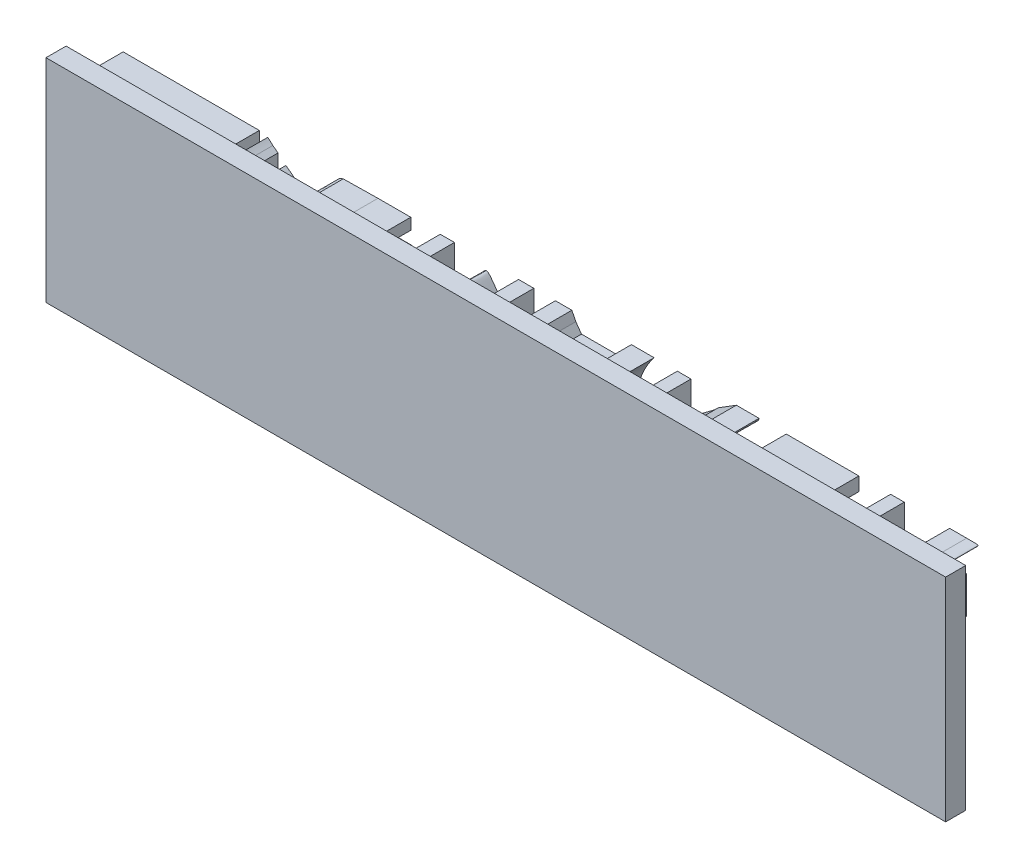
SolidWorks part; units mm, degrees
ref_plane "Front Plane" through (0, 0, 0) normal (0, 0, 1) x (1, 0, 0)
ref_plane "Top Plane" through (0, 0, 0) normal (0, 1, 0) x (1, 0, 0)
ref_plane "Right Plane" through (0, 0, 0) normal (1, 0, 0) x (0, 0, -1)
sketch "Sketch1" plane through (0, 0, 0) normal (0, 0, 1) x (1, 0, 0)
  line L3 (5.334, 288.4593) -> (5.0518, 287.3304)
  line L4 (5.0518, 287.3304) -> (5.0518, 276.606)
  line L5 (5.0518, 276.606) -> (5.0518, 266.4178)
  line L6 (5.0518, 266.4178) -> (5.334, 265.0067)
  line L7 (7.5918, 263.0311) -> (8.7207, 262.4667)
  line L8 (8.7207, 262.4667) -> (23.7349, 262.4667)
  line L9 (23.7349, 262.4667) -> (38.6644, 262.4667)
  line L10 (38.6644, 262.4667) -> (39.7933, 263.0311)
  line L11 (42.3333, 272.6549) -> (42.3333, 279.4282)
  line L12 (42.3333, 279.4282) -> (27.1498, 279.4282)
  line L13 (27.1498, 279.4282) -> (11.9944, 279.4282)
  line L14 (11.9944, 279.4282) -> (11.9944, 282.5327)
  line L15 (11.9944, 282.5327) -> (11.9944, 285.6371)
  line L16 (11.9944, 285.6371) -> (27.1498, 285.6371)
  line L17 (27.1498, 285.6371) -> (42.3333, 285.6371)
  line L18 (42.3333, 285.6371) -> (42.3333, 288.4593)
  line L19 (42.3333, 288.4593) -> (42.3333, 291.2816)
  line L20 (42.3333, 291.2816) -> (26.0209, 291.2816)
  line L21 (35.2778, 270.6793) -> (35.2778, 267.5467)
  line L22 (35.2778, 267.5467) -> (23.5091, 267.5467)
  line L23 (23.5091, 267.5467) -> (11.9944, 267.5467)
  line L24 (11.9944, 267.5467) -> (11.7687, 270.3971)
  line L25 (23.5091, 273.7838) -> (35.2778, 273.7838)
  line L26 (35.2778, 273.7838) -> (35.2778, 270.6793)
  line L27 (57.0089, 273.5016) -> (57.0089, 255.6933)
  line L28 (57.0089, 255.6933) -> (60.6778, 255.6933)
  line L29 (60.6778, 255.6933) -> (64.0644, 255.6933)
  line L30 (64.0644, 255.6933) -> (72.2489, 266.4178)
  line L31 (88.9, 266.4178) -> (96.8022, 255.6933)
  line L32 (96.8022, 255.6933) -> (100.1889, 255.6933)
  line L33 (100.1889, 255.6933) -> (103.5756, 255.6933)
  line L34 (103.5756, 255.6933) -> (103.5756, 273.5016)
  line L35 (103.5756, 273.5016) -> (103.5756, 291.2816)
  line L36 (103.5756, 291.2816) -> (99.9067, 291.2816)
  line L37 (99.9067, 291.2816) -> (95.9556, 291.2816)
  line L38 (95.9556, 291.2816) -> (95.9556, 278.5816)
  line L39 (95.9556, 278.5816) -> (96.2378, 265.8533)
  line L40 (96.2378, 265.8533) -> (95.3911, 267.2644)
  line L41 (64.0644, 278.8638) -> (64.0644, 291.2816)
  line L42 (64.0644, 291.2816) -> (60.6778, 291.2816)
  line L43 (60.6778, 291.2816) -> (57.0089, 291.2816)
  line L44 (57.0089, 291.2816) -> (57.0089, 273.5016)
  line L45 (124.1778, 273.2193) -> (134.0556, 255.6933)
  line L46 (134.0556, 255.6933) -> (138.5711, 255.6933)
  line L47 (138.5711, 255.6933) -> (143.0867, 255.6933)
  line L48 (143.0867, 255.6933) -> (145.3444, 261.62)
  line L49 (158.8911, 291.2816) -> (152.1178, 291.2816)
  line L50 (152.1178, 291.2816) -> (152.1178, 287.3304)
  line L51 (152.1178, 287.3304) -> (149.86, 283.3793)
  line L52 (149.86, 283.3793) -> (138.5711, 283.3793)
  line L53 (138.5711, 283.3793) -> (127.2822, 283.3793)
  line L54 (127.2822, 283.3793) -> (124.46, 287.3304)
  line L55 (124.46, 287.3304) -> (122.4844, 291.2816)
  line L56 (122.4844, 291.2816) -> (118.2511, 291.2816)
  line L57 (145.3444, 276.8882) -> (138.5711, 262.7489)
  line L58 (174.9778, 273.5016) -> (174.9778, 255.6933)
  line L59 (174.9778, 255.6933) -> (177.2356, 255.6933)
  line L60 (177.2356, 255.6933) -> (181.7511, 255.6933)
  line L61 (181.7511, 255.6933) -> (181.7511, 263.0311)
  line L62 (181.7511, 263.0311) -> (181.7511, 270.3971)
  line L63 (181.7511, 270.3971) -> (193.04, 263.0311)
  line L64 (193.04, 263.0311) -> (202.0711, 255.6933)
  line L65 (202.0711, 255.6933) -> (208.8444, 255.6933)
  line L66 (208.8444, 255.6933) -> (213.36, 255.9756)
  line L67 (213.36, 255.9756) -> (202.0711, 264.16)
  line L68 (211.1022, 291.2816) -> (204.3289, 291.2816)
  line L69 (204.3289, 291.2816) -> (195.2978, 285.6371)
  line L70 (186.2667, 278.0171) -> (181.7511, 275.7593)
  line L71 (181.7511, 275.7593) -> (181.7511, 283.3793)
  line L72 (181.7511, 283.3793) -> (181.7511, 291.2816)
  line L73 (181.7511, 291.2816) -> (177.2356, 291.2816)
  line L74 (177.2356, 291.2816) -> (174.9778, 291.2816)
  line L75 (174.9778, 291.2816) -> (174.9778, 273.5016)
  line L76 (229.1644, 273.5016) -> (229.1644, 255.6933)
  line L77 (229.1644, 255.6933) -> (247.2267, 255.6933)
  line L78 (247.2267, 255.6933) -> (265.2889, 255.6933)
  line L79 (265.2889, 255.6933) -> (265.2889, 258.7978)
  line L80 (265.2889, 258.7978) -> (265.2889, 261.9022)
  line L81 (265.2889, 261.9022) -> (251.7422, 261.9022)
  line L82 (251.7422, 261.9022) -> (235.9378, 261.9022)
  line L83 (235.9378, 261.9022) -> (235.9378, 265.8533)
  line L84 (235.9378, 265.8533) -> (235.9378, 269.8327)
  line L85 (235.9378, 269.8327) -> (244.9689, 269.8327)
  line L86 (244.9689, 269.8327) -> (254, 269.8327)
  line L87 (254, 269.8327) -> (254, 272.9371)
  line L88 (254, 272.9371) -> (254, 275.7593)
  line L89 (254, 275.7593) -> (244.9689, 275.7593)
  line L90 (244.9689, 275.7593) -> (235.9378, 275.7593)
  line L91 (235.9378, 275.7593) -> (235.9378, 280.2749)
  line L92 (235.9378, 280.2749) -> (235.9378, 284.5082)
  line L93 (235.9378, 284.5082) -> (251.7422, 284.5082)
  line L94 (251.7422, 284.5082) -> (265.2889, 284.5082)
  line L95 (265.2889, 284.5082) -> (265.2889, 287.8949)
  line L96 (265.2889, 287.8949) -> (265.2889, 291.2816)
  line L97 (265.2889, 291.2816) -> (247.2267, 291.2816)
  line L98 (247.2267, 291.2816) -> (229.1644, 291.2816)
  line L99 (229.1644, 291.2816) -> (229.1644, 273.5016)
  line L100 (281.0933, 273.2193) -> (281.0933, 255.6933)
  line L101 (281.0933, 255.6933) -> (296.3333, 255.6933)
  line L102 (310.4444, 277.7349) -> (304.8, 278.0171)
  line L103 (304.8, 278.0171) -> (316.0889, 284.226)
  line L104 (318.9111, 291.2816) -> (310.4444, 291.2816)
  line L105 (310.4444, 291.2816) -> (304.8, 284.5082)
  line L106 (304.8, 284.5082) -> (296.3333, 277.7349)
  line L107 (296.3333, 277.7349) -> (293.5111, 277.7349)
  line L108 (293.5111, 277.7349) -> (287.8667, 278.0171)
  line L109 (287.8667, 278.0171) -> (287.8667, 284.5082)
  line L110 (287.8667, 284.5082) -> (287.8667, 291.2816)
  line L111 (287.8667, 291.2816) -> (285.0444, 291.2816)
  line L112 (285.0444, 291.2816) -> (281.0933, 291.2816)
  line L113 (281.0933, 291.2816) -> (281.0933, 273.2193)
  line L114 (299.1556, 261.9022) -> (287.8667, 261.9022)
  line L115 (287.8667, 261.9022) -> (287.8667, 266.7)
  line L116 (287.8667, 266.7) -> (287.8667, 271.8082)
  line L117 (287.8667, 271.8082) -> (299.1556, 271.8082)
  line L118 (299.1556, 271.8082) -> (310.4444, 271.8082)
  line L119 (310.4444, 271.8082) -> (310.4444, 270.9616)
  line L120 (-100.7533, 257.1044) -> (-100.7533, 223.2378)
  line L121 (-100.7533, 223.2378) -> (-66.8867, 223.2378)
  line L122 (-66.8867, 223.2378) -> (-33.02, 223.2378)
  line L123 (-33.02, 223.2378) -> (-33.02, 231.7044)
  line L124 (-33.02, 231.7044) -> (-33.02, 239.8889)
  line L125 (-33.02, 239.8889) -> (-56.4444, 239.8889)
  line L126 (-56.4444, 239.8889) -> (-80.1511, 239.8889)
  line L127 (-80.1511, 239.8889) -> (-80.1511, 245.2511)
  line L128 (-80.1511, 245.2511) -> (-80.1511, 250.3311)
  line L129 (-80.1511, 250.3311) -> (-56.4444, 250.3311)
  line L130 (-56.4444, 250.3311) -> (-33.02, 250.3311)
  line L131 (-33.02, 250.3311) -> (-33.02, 257.9511)
  line L132 (-33.02, 257.9511) -> (-33.02, 265.2889)
  line L133 (-33.02, 265.2889) -> (-56.4444, 265.2889)
  line L134 (-56.4444, 265.2889) -> (-80.1511, 265.2889)
  line L135 (-80.1511, 265.2889) -> (-80.1511, 270.9616)
  line L136 (-80.1511, 270.9616) -> (-80.1511, 276.0416)
  line L137 (-80.1511, 276.0416) -> (-56.4444, 276.0416)
  line L138 (-56.4444, 276.0416) -> (-33.02, 276.0416)
  line L139 (-33.02, 276.0416) -> (-33.02, 283.3793)
  line L140 (-33.02, 283.3793) -> (-33.02, 290.9993)
  line L141 (-33.02, 290.9993) -> (-66.8867, 290.9993)
  line L142 (-66.8867, 290.9993) -> (-100.7533, 290.9993)
  line L143 (-100.7533, 290.9993) -> (-100.7533, 257.1044)
  line L144 (-29.0689, 256.54) -> (-29.0689, 222.9556)
  line L145 (-29.0689, 222.9556) -> (-18.6549, 214.4889)
  line L146 (-7.0838, 238.76) -> (-7.0838, 272.0904)
  line L147 (-7.0838, 272.0904) -> (-8.7771, 273.7838)
  line L148 (-8.7771, 273.7838) -> (-10.7527, 275.4771)
  line L149 (-10.7527, 275.4771) -> (-10.7527, 252.0244)
  line L150 (-13.0104, 230.8578) -> (-15.2682, 232.2689)
  line L151 (-15.2682, 232.2689) -> (-15.2682, 255.6933)
  line L152 (-15.2682, 255.6933) -> (-15.2682, 279.146)
  line L153 (-15.2682, 279.146) -> (-17.526, 280.8393)
  line L154 (-17.526, 280.8393) -> (-19.7838, 282.5327)
  line L155 (-19.7838, 282.5327) -> (-19.7838, 259.08)
  line L156 (-19.7838, 259.08) -> (-19.7838, 235.9378)
  line L157 (-19.7838, 235.9378) -> (-21.7593, 237.6311)
  line L158 (-21.7593, 237.6311) -> (-23.7349, 239.0422)
  line L159 (-23.7349, 239.0422) -> (-23.7349, 262.4667)
  line L160 (-23.7349, 262.4667) -> (-23.7349, 285.9193)
  line L161 (-23.7349, 285.9193) -> (-26.2749, 287.8949)
  line L162 (-86.0778, 211.9489) -> (-73.0956, 203.2)
  line L163 (-73.0956, 203.2) -> (-41.2044, 203.2)
  line L164 (-41.2044, 203.2) -> (-9.0593, 203.2)
  line L165 (-9.0593, 203.2) -> (-11.8816, 205.4578)
  line L166 (-11.8816, 205.4578) -> (-14.1393, 207.4333)
  line L167 (-14.1393, 207.4333) -> (-36.6889, 207.4333)
  line L168 (-36.6889, 207.4333) -> (-59.5489, 207.4333)
  line L169 (-59.5489, 207.4333) -> (-61.2422, 208.8444)
  line L170 (-61.2422, 208.8444) -> (-62.9356, 209.9733)
  line L171 (-62.9356, 209.9733) -> (-40.64, 210.2556)
  line L172 (-40.64, 210.2556) -> (-18.0904, 210.2556)
  line L173 (-18.0904, 210.2556) -> (-20.3482, 212.2311)
  line L174 (-20.3482, 212.2311) -> (-22.8882, 213.9244)
  line L175 (-22.8882, 213.9244) -> (-45.72, 213.9244)
  line L176 (-45.72, 213.9244) -> (-68.58, 213.9244)
  line L177 (-68.58, 213.9244) -> (-70.8378, 215.3356)
  line L178 (-70.8378, 215.3356) -> (-72.5311, 216.7467)
  line L179 (-72.5311, 216.7467) -> (-49.3889, 216.7467)
  line L180 (-49.3889, 216.7467) -> (-26.5571, 216.7467)
  line L181 (-26.5571, 216.7467) -> (-28.7867, 218.7222)
  line L182 (-28.7867, 218.7222) -> (-31.0444, 220.6978)
  line L183 (-31.0444, 220.6978) -> (-65.1933, 220.6978)
  line L184 (-65.1933, 220.6978) -> (-99.06, 220.6978)
  line L185 (-99.06, 220.6978) -> (-86.0778, 211.9489)
  spline S0 degree 3 poles (8.7207, 290.9993) (7.0273, 290.4349) (6.1807, 289.8704) (5.334, 288.4593) knots 0 0 0 0 1 1 1 1
  spline S1 degree 3 poles (5.334, 265.0067) (6.1807, 263.5956) (6.4629, 263.3133) (7.5918, 263.0311) knots 0 0 0 0 1 1 1 1
  spline S2 degree 3 poles (39.7933, 263.0311) (40.9222, 263.3133) (41.2044, 263.8778) (41.4867, 264.7244) knots 0 0 0 0 1 1 1 1
  spline S3 degree 3 poles (41.4867, 264.7244) (42.0511, 265.5711) (42.3333, 265.8533) (42.3333, 272.6549) knots 0 0 0 0 1 1 1 1
  spline S4 degree 3 poles (26.0209, 291.2816) (16.9616, 291.2816) (9.2851, 290.9993) (8.7207, 290.9993) knots 0 0 0 0 1 1 1 1
  spline S5 degree 3 poles (11.7687, 270.3971) (11.7687, 272.0904) (11.7687, 273.2193) (11.7687, 273.5016) knots 0 0 0 0 1 1 1 1
  spline S6 degree 3 poles (11.7687, 273.5016) (11.9944, 273.7838) (14.2522, 273.7838) (23.5091, 273.7838) knots 0 0 0 0 1 1 1 1
  spline S7 degree 3 poles (72.2489, 266.4178) (76.7644, 272.0904) (80.7156, 277.1704) (80.7156, 276.8882) knots 0 0 0 0 1 1 1 1
  spline S8 degree 2 poles (80.7156, 276.8882) (84.3844, 272.0904) (88.9, 266.4178) knots 0 0 0 1 1 1
  spline S9 degree 3 poles (95.3911, 267.2644) (94.8267, 268.1393) (91.44, 272.9371) (87.7711, 277.7349) knots 0 0 0 0 1 1 1 1
  spline S10 degree 3 poles (87.7711, 277.7349) (80.9978, 287.0482) (80.9978, 287.0482) (79.8689, 287.0482) knots 0 0 0 0 1 1 1 1
  spline S11 degree 3 poles (79.8689, 287.0482) (79.3044, 287.0482) (79.0222, 287.0482) (72.5311, 278.0171) knots 0 0 0 0 1 1 1 1
  spline S12 degree 3 poles (72.5311, 278.0171) (68.58, 273.2193) (65.1933, 268.4216) (64.9111, 267.5467) knots 0 0 0 0 1 1 1 1
  spline S13 degree 3 poles (64.9111, 267.5467) (64.3467, 266.7) (64.0644, 266.4178) (64.0644, 266.1356) knots 0 0 0 0 1 1 1 1
  spline S14 degree 2 poles (64.0644, 266.1356) (64.0644, 271.8082) (64.0644, 278.8638) knots 0 0 0 1 1 1
  spline S15 degree 3 poles (114.3, 291.2816) (114.3, 290.9993) (118.8156, 283.0971) (124.1778, 273.2193) knots 0 0 0 0 1 1 1 1
  spline S16 degree 3 poles (145.3444, 261.62) (147.6022, 265.0067) (152.1178, 272.9371) (156.6333, 279.146) knots 0 0 0 0 1 1 1 1
  spline S17 degree 2 poles (156.6333, 279.146) (158.8911, 285.6371) (163.4067, 291.2816) knots 0 0 0 1 1 1
  spline S18 degree 2 poles (163.4067, 291.2816) (161.1489, 291.2816) (158.8911, 291.2816) knots 0 0 0 1 1 1
  spline S19 degree 2 poles (118.2511, 291.2816) (115.9933, 291.2816) (114.3, 291.2816) knots 0 0 0 1 1 1
  spline S20 degree 3 poles (138.5711, 262.7489) (138.5711, 263.0311) (129.54, 276.8882) (129.54, 277.1704) knots 0 0 0 0 1 1 1 1
  spline S21 degree 2 poles (129.54, 277.1704) (134.0556, 277.1704) (138.5711, 277.1704) knots 0 0 0 1 1 1
  spline S22 degree 3 poles (138.5711, 277.1704) (143.0867, 277.1704) (145.3444, 277.1704) (145.3444, 276.8882) knots 0 0 0 0 1 1 1 1
  spline S23 degree 2 poles (202.0711, 264.16) (195.2978, 268.7038) (190.7822, 272.3727) knots 0 0 0 1 1 1
  spline S24 degree 3 poles (190.7822, 272.3727) (190.7822, 272.6549) (202.0711, 280.5571) (211.1022, 287.6127) knots 0 0 0 0 1 1 1 1
  spline S25 degree 3 poles (211.1022, 287.6127) (215.6178, 289.306) (215.6178, 290.9993) (215.6178, 291.2816) knots 0 0 0 0 1 1 1 1
  spline S26 degree 2 poles (215.6178, 291.2816) (213.36, 291.2816) (211.1022, 291.2816) knots 0 0 0 1 1 1
  spline S27 degree 3 poles (195.2978, 285.6371) (193.04, 282.8149) (186.2667, 279.146) (186.2667, 278.0171) knots 0 0 0 0 1 1 1 1
  spline S28 degree 3 poles (296.3333, 255.6933) (316.0889, 255.9756) (316.0889, 255.6933) (318.9111, 257.6689) knots 0 0 0 0 1 1 1 1
  spline S29 degree 3 poles (318.9111, 257.6689) (318.9111, 259.08) (318.9111, 259.9267) (318.9111, 267.5467) knots 0 0 0 0 1 1 1 1
  spline S30 degree 3 poles (318.9111, 267.5467) (318.9111, 274.3482) (318.9111, 274.3482) (318.9111, 275.7593) knots 0 0 0 0 1 1 1 1
  spline S31 degree 3 poles (318.9111, 275.7593) (316.0889, 277.4527) (316.0889, 277.7349) (310.4444, 277.7349) knots 0 0 0 0 1 1 1 1
  spline S32 degree 3 poles (316.0889, 284.226) (318.9111, 287.6127) (324.5556, 290.4349) (324.5556, 290.7171) knots 0 0 0 0 1 1 1 1
  spline S33 degree 3 poles (324.5556, 290.7171) (324.5556, 291.2816) (324.5556, 291.2816) (318.9111, 291.2816) knots 0 0 0 0 1 1 1 1
  spline S34 degree 3 poles (310.4444, 270.9616) (310.4444, 270.3971) (310.4444, 270.3971) (310.4444, 267.2644) knots 0 0 0 0 1 1 1 1
  spline S35 degree 3 poles (310.4444, 267.2644) (310.4444, 263.5956) (310.4444, 263.0311) (310.4444, 262.1844) knots 0 0 0 0 1 1 1 1
  spline S36 degree 3 poles (310.4444, 262.1844) (307.6222, 261.9022) (307.6222, 261.9022) (299.1556, 261.9022) knots 0 0 0 0 1 1 1 1
  spline S37 degree 3 poles (-18.6549, 214.4889) (-12.7282, 209.9733) (-7.6482, 206.0222) (-7.366, 206.0222) knots 0 0 0 0 1 1 1 1
  spline S38 degree 3 poles (-7.366, 206.0222) (-7.0838, 205.74) (-7.0838, 206.5867) (-7.0838, 238.76) knots 0 0 0 0 1 1 1 1
  spline S39 degree 3 poles (-10.7527, 252.0244) (-10.7527, 239.6067) (-10.7527, 229.1644) (-11.0349, 229.1644) knots 0 0 0 0 1 1 1 1
  spline S40 degree 2 poles (-11.0349, 229.1644) (-11.8816, 229.7289) (-13.0104, 230.8578) knots 0 0 0 1 1 1
  spline S41 degree 2 poles (-26.2749, 287.8949) (-27.686, 289.0238) (-28.7867, 290.1527) knots 0 0 0 1 1 1
  spline S42 degree 3 poles (-28.7867, 290.1527) (-29.0689, 290.1527) (-29.0689, 283.3793) (-29.0689, 256.54) knots 0 0 0 0 1 1 1 1
extrude "Boss-Extrude1" add sketch "Sketch1" against normal blind 20
sketch "Sketch2" plane through (0, 0, 0) normal (0, 0, 1) x (1, 0, 0)
  line L1 (-109.1502, 299.2832) -> (338.4477, 299.2832)
  line L2 (-109.1502, 299.2832) -> (-109.1502, 193.7823)
  line L3 (-109.1502, 193.7823) -> (338.4477, 193.7823)
  line L4 (338.4477, 299.2832) -> (338.4477, 193.7823)
extrude "Boss-Extrude2" add sketch "Sketch2" along normal blind 10
